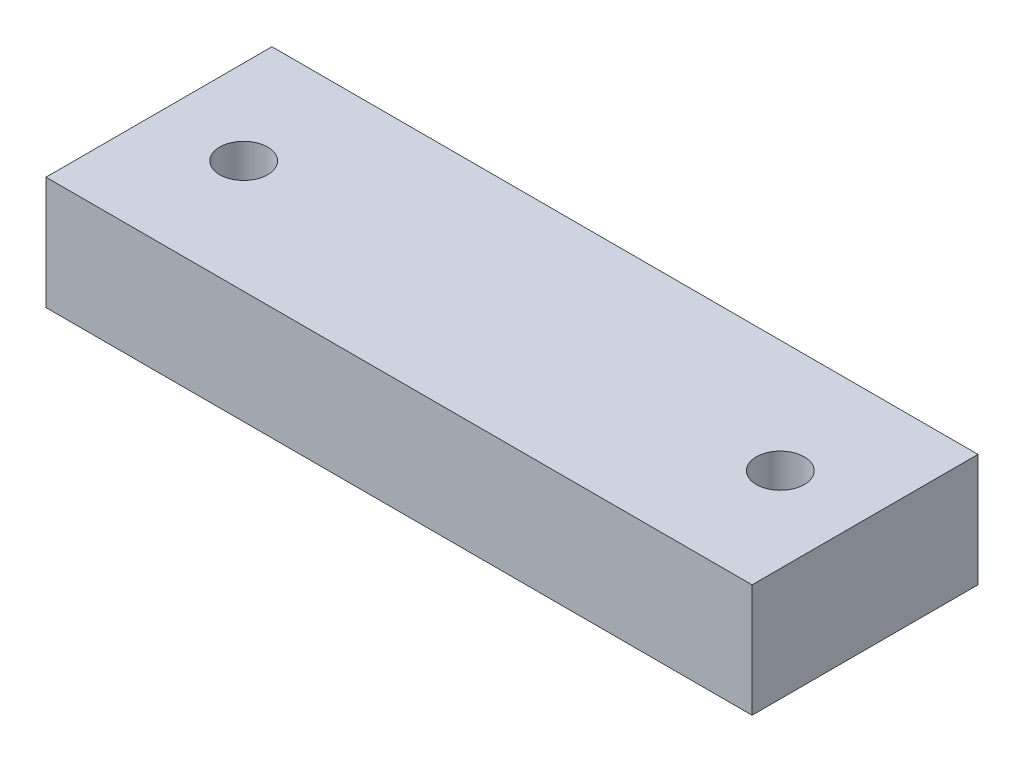
SolidWorks part; units mm, degrees
ref_plane "前视基准面" through (0, 0, 0) normal (0, 0, 1) x (1, 0, 0)
ref_plane "上视基准面" through (0, 0, 0) normal (0, 1, 0) x (1, 0, 0)
ref_plane "右视基准面" through (0, 0, 0) normal (1, 0, 0) x (0, 0, -1)
sketch "草图1" plane through (0, 0, 0) normal (0, 1, 0) x (1, 0, 0)
  line L1 (-62.5, 20) -> (62.5, 20)
  line L2 (-62.5, 20) -> (-62.5, -20)
  line L3 (-62.5, -20) -> (62.5, -20)
  line L4 (62.5, 20) -> (62.5, -20)
  line L5 (-62.5, 20) -> (62.5, -20) construction
  line L6 (-62.5, -20) -> (62.5, 20) construction
  point P0 (0, 0)
  dimension "D1" = 125
  dimension "D2" = 40
extrude "凸台-拉伸1" add sketch "草图1" along normal blind 20
sketch "草图2" plane through (0, 20, 0) normal (0, 1, 0) x (1, 0, 0)
  line L0 (47.5, 0) -> (-47.5, 0) construction
  line L2 (0, 36.4384) -> (0, -29.528) construction
  point P7 (0, 0)
  dimension "D1" = 95
hole_wizard "M10 螺纹孔1" positions "草图4" profile "草图5" tap size "M10" standard "GB"
sketch "草图4" plane through (0, 20, 0) normal (0, 1, 0) x (1, 0, 0)
  point P1 (47.5, 0)
  point P4 (-47.5, 0)
sketch "草图5" plane through (47.5, 20, 0) normal (1, 0, 0) x (0, 0, 1)
  line L0 (0, 0) -> (0, 27.0537)
  line L1 (0, 27.0537) -> (4.25, 24.5)
  line L2 (4.25, 24.5) -> (4.25, 0)
  line L5 (4.25, 0) -> (0, 0)
  line L10 (0, 27.0537) -> (-4.25, 24.5) construction
  line L11 (0, -6.35) -> (0, 107.95) construction
  dimension "螺纹孔钻头直径" = 8.5
  dimension "螺纹孔钻头深度" = 24.5
  dimension "导头角度" = 118
cosmetic thread "孔螺蚊线1"
cosmetic thread "孔螺蚊线2"
